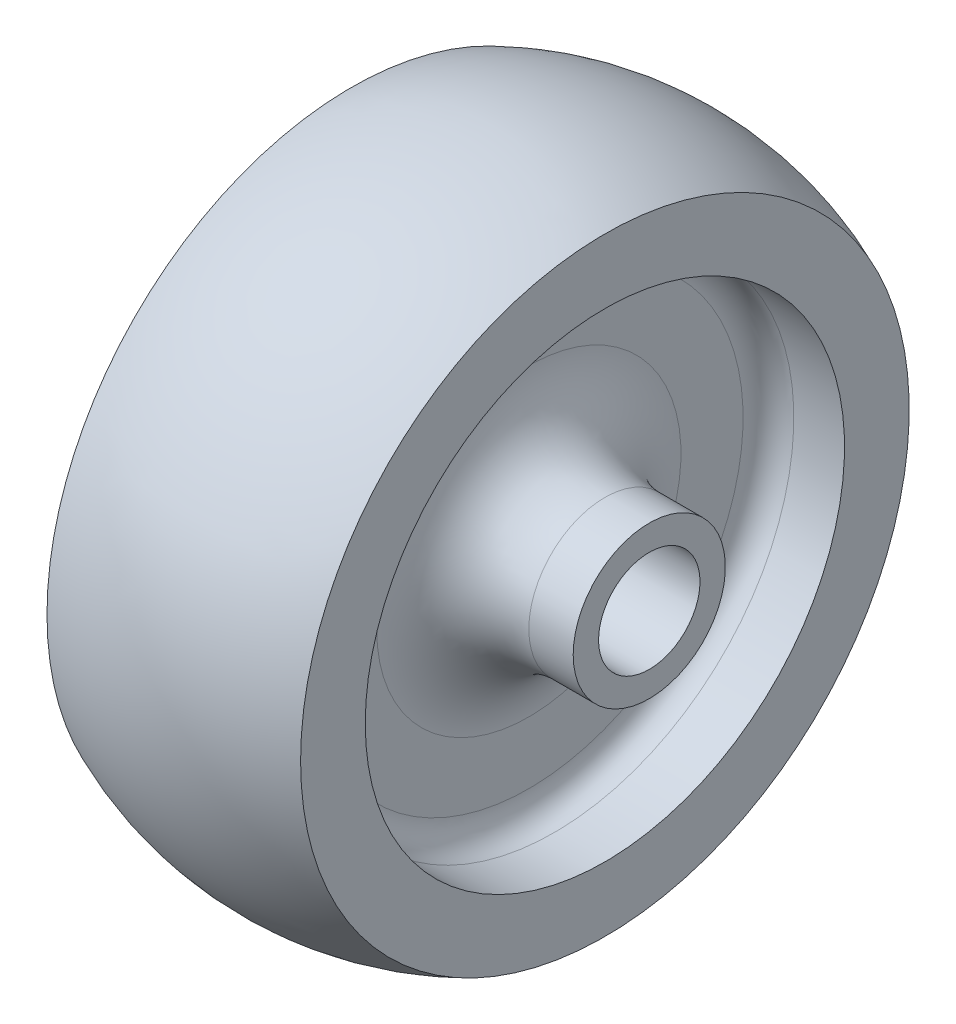
SolidWorks part; units mm, degrees
ref_plane "Front Plane" through (0, 0, 0) normal (0, 0, 1) x (1, 0, 0)
ref_plane "Top Plane" through (0, 0, 0) normal (0, 1, 0) x (1, 0, 0)
ref_plane "Right Plane" through (0, 0, 0) normal (1, 0, 0) x (0, 0, -1)
sketch "Sketch1" plane through (0, 0, 0) normal (0, 0, 1) x (1, 0, 0)
  line L0 (0, 0) -> (21.0336, 0) construction
  line L1 (0, 4) -> (0, 6)
  line L4 (0, 4) -> (27, 4)
  line L6 (0, 6) -> (3.5, 6)
  line L7 (3.5, 18.9) -> (3.5, 24)
  line L8 (23.5, 24) -> (23.5, 18.9)
  line L9 (23.5, 6) -> (27, 6)
  line L10 (27, 6) -> (27, 4)
  line L12 (3.5, 6) -> (9.5, 6)
  line L14 (3.5, 18.9) -> (7.5, 18.9)
  line L15 (9.5, 6) -> (9.5, 16.9)
  line L16 (23.5, 6) -> (17.5, 6)
  line L18 (23.5, 18.9) -> (19.5, 18.9)
  line L19 (17.5, 6) -> (17.5, 16.9)
  arc A0 (3.5, 24) -> (23.5, 24) centre (13.5, 1.0871) cw
  arc A1 (19.5, 18.9) -> (17.5, 16.9) centre (19.5, 16.9) ccw
  arc A2 (7.5, 18.9) -> (9.5, 16.9) centre (7.5, 16.9) cw
  point P20 (17.5, 18.9)
  point P23 (9.5, 18.9)
  dimension "D11" = 25
  dimension "D12" = 2
  dimension "D1" = 8
  dimension "D2" = 27
  dimension "D3" = 20
  dimension "D4" = 3.5
  dimension "D5" = 12
  dimension "D6" = 12
  dimension "D7" = 6
  dimension "D8" = 6
  dimension "D9" = 37.8
  dimension "D10" = 37.8
  dimension "D13" = 48
  dimension "D14" = 48
revolve "Revolve1" add sketch "Sketch1" angle 360 about L0
fillet "Fillet1" radius 6 2 edges at (17.5, 0, 6) (9.5, 0, 6)
scale "Scale1" scale about origin uniform scaling yes scale factor 0.5
